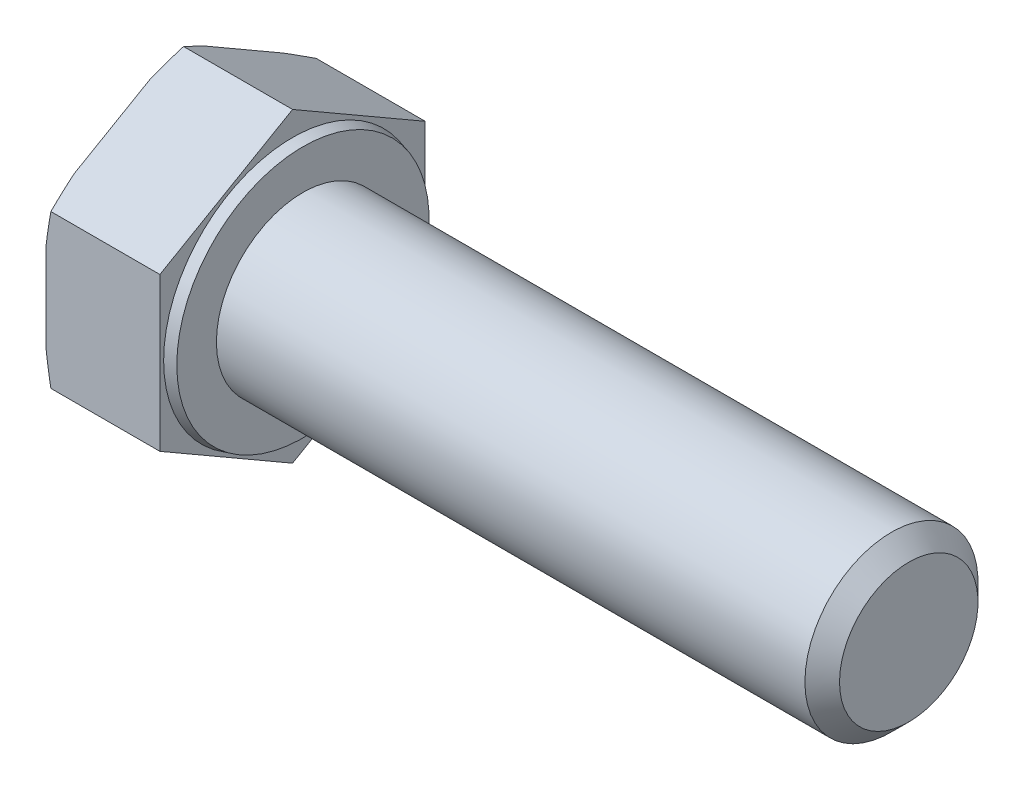
SolidWorks part; units mm, degrees
material "AISI 1020"
ref_plane "Спереди" through (0, 0, 0) normal (0, 0, 1) x (1, 0, 0)
ref_plane "Сверху" through (0, 0, 0) normal (0, 1, 0) x (1, 0, 0)
ref_plane "Справа" through (0, 0, 0) normal (1, 0, 0) x (0, 0, -1)
sketch "Эскиз1" plane through (0, 0, 0) normal (0, 0, 1) x (1, 0, 0)
  line L0 (-1000, 0) -> (49000, 0) construction
  line L1 (-6.58, 0) -> (-6.58, 8.85)
  line L2 (-6.58, 8.85) -> (0, 8.85)
  line L3 (0, 8.85) -> (0, 7.449)
  line L4 (0.6, 5) -> (35.6, 5)
  line L5 (35.6, 5) -> (35.6, 0)
  line L6 (-6.58, 0) -> (35.6, 0)
  line L7 (0, 7.449) -> (0.6, 7.2882)
  line L8 (0.6, 7.2882) -> (0.6, 5)
  line L9 (0.5, 0) -> (0.5, 7.315) construction
  dimension "_d" = 10
  dimension "D1" = 35
  dimension "D5" = 17.7
  dimension "D2" = 0.6
  dimension "D3" = 6.58
  dimension "D4" = 0.1
  dimension "D6" = 14.63
  dimension "D7" = 75
revolve "Повернуть1" add sketch "Эскиз1" angle 360 about L0
cosmetic thread "Условное изображение резьбы1" parameters "D1"=26, "D2"=8.344
sketch "Эскиз2" plane through (-6.58, 0, 0) normal (-1, 0, 0) x (0, 0, 1)
  line L1 (0, -8.85) -> (7.6643, -4.425)
  line L2 (7.6643, -4.425) -> (7.6643, 4.425)
  line L3 (7.6643, 4.425) -> (0, 8.85)
  line L4 (0, 8.85) -> (-7.6643, 4.425)
  line L5 (-7.6643, 4.425) -> (-7.6643, -4.425)
  line L6 (-7.6643, -4.425) -> (0, -8.85)
  circle A0 centre (0, 0) radius 7.6643 construction
  circle A1 centre (0, 0) radius 8.85 construction
extrude "Вырез-Вытянуть1" cut sketch "Эскиз2" against normal through all flip side to cut
sketch "Эскиз4" plane through (0, 0, 0) normal (0, 0, 1) x (1, 0, 0)
  line L0 (-1000, 0) -> (49000, 0) construction
  line L1 (-6.58, 8.075) -> (-6.2979, 8.85)
  line L2 (-6.2979, 8.85) -> (-6.58, 8.85)
  line L3 (-6.58, 8.85) -> (-6.58, 8.075)
  line L4 (-6.58, 4.425) -> (-6.58, 8.85) construction
  line L6 (0, 8.85) -> (-6.58, 8.85) construction
  dimension "D1" = 20
  dimension "D2" = 16.15
revolve "Вырез-Повернуть1" cut sketch "Эскиз4" angle 360 about L0
chamfer "Фаска1" distance 1 angle 45 1 edges at (35.6, 0, 5)
equation "\"l\"= 35'длина болта"
equation "\"_d\"= 10'диаметр болта"
equation "\"b\"= 20'длина резьбы"
equation "\"k\"= 6.58'толщина шляпки"
equation "\"e\"= 17.7'диаметр головки описанный"
equation "\"S\"= 17'размер под ключ"
equation "\"_d@Эскиз1\"=\"_d\""
equation "\"dw\"= 14.63"
equation "\"da\"= 9.78"
equation "\"с\"= 0.6"
equation "\"D1@Эскиз1\"=\"l\""
equation "\"D5@Эскиз1\"=\"e\""
equation "\"D2@Эскиз1\"=\"с\""
equation "\"D3@Эскиз1\"=\"k\""
equation "\"D2@Эскиз4\"=\"S\"*0.95"
equation "\"D1@Фаска1\"=\"_d\"/10"
equation "\"D6@Эскиз1\"=\"dw\""
